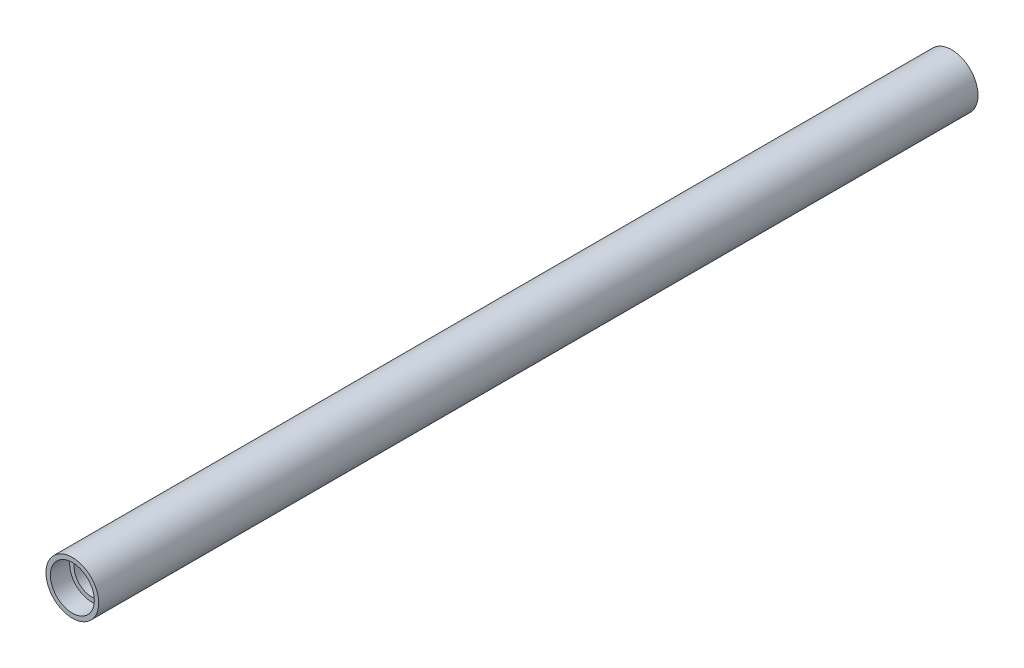
SolidWorks part; units mm, degrees
ref_plane "Front Plane" through (0, 0, 0) normal (0, 0, 1) x (1, 0, 0)
ref_plane "Top Plane" through (0, 0, 0) normal (0, 1, 0) x (1, 0, 0)
ref_plane "Right Plane" through (0, 0, 0) normal (1, 0, 0) x (0, 0, -1)
sketch "Sketch1" plane through (0, 0, 0) normal (0, 0, 1) x (1, 0, 0)
  circle A0 centre (0, 0) radius 7.5
  circle A1 centre (0, 0) radius 5
  dimension "D1" = 15
  dimension "D2" = 10
extrude "Boss-Extrude1" add sketch "Sketch1" along normal mid plane 250
sketch "Sketch2" plane through (0, 0, 125) normal (0, 0, 1) x (1, 0, 0)
  circle A0 centre (0, 0) radius 6.25
  dimension "D1" = 12.5
extrude "Cut-Extrude1" cut sketch "Sketch2" against normal blind 5.5
mirror "Mirror1" about plane through (0, 0, 0) normal (0, 0, 1) of "Cut-Extrude1"
